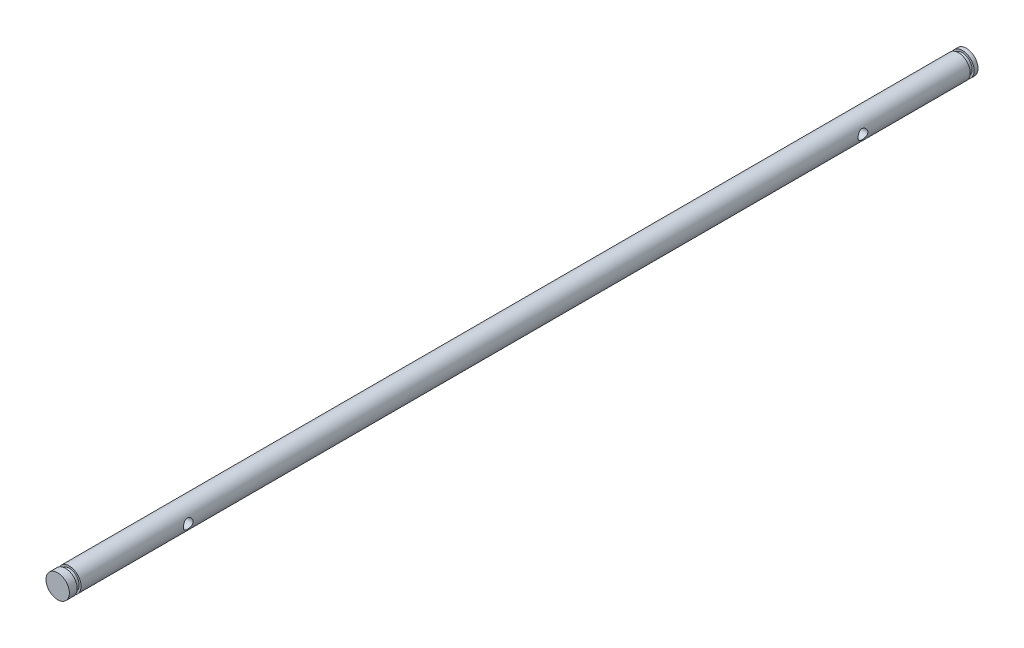
SolidWorks part; units mm, degrees
ref_plane "Front Plane" through (0, 0, 0) normal (0, 0, 1) x (1, 0, 0)
ref_plane "Top Plane" through (0, 0, 0) normal (0, 1, 0) x (1, 0, 0)
ref_plane "Right Plane" through (0, 0, 0) normal (1, 0, 0) x (0, 0, -1)
sketch "Sketch1" plane through (0, 0, 0) normal (0, 0, 1) x (1, 0, 0)
  circle A0 centre (0, 0) radius 3
  dimension "D1" = 6
extrude "Boss-Extrude1" add sketch "Sketch1" along normal blind 233
ref_axis "Axis1" through (0, 0, 233) along (0, 0, -1)
sketch "Sketch2" plane through (0, 0, 0) normal (0, 1, 0) x (1, 0, 0)
  line L0 (3, -233) -> (3, 0) construction
  line L1 (3, -1) -> (2.5, -1)
  line L2 (3, -1) -> (3, -2)
  line L3 (3, -2) -> (2.5, -2)
  line L4 (2.5, -1) -> (2.5, -2)
  line L5 (3, 0) -> (-3, 0) construction
  dimension "D1" = 1
  dimension "D2" = 0.5
  dimension "D3" = 1
revolve "Cut-Revolve1" cut sketch "Sketch2" angle 360 about axis through (0, 0, 233) along (0, 0, -1)
sketch "Sketch3" plane through (0, 0, 233) normal (0, 0, 1) x (1, 0, 0)
  line L0 (2.7, 1.3077) -> (2.7, -1.3077)
  circle A0 centre (0, 0) radius 3 construction
  circle A1 centre (0, 0) radius 3
  arc A2 (2.7, -1.3077) -> (2.7, 1.3077) centre (0, 0) ccw
  dimension "D2" = 2.7
  dimension "D1" = 0
extrude "Cut-Extrude1" cut sketch "Sketch3" against normal blind 0.5
ref_plane "Plane1" through (3.7, 0, 0) normal (1, 0, 0) x (0, 0, -1)
sketch "Sketch4" plane through (3.7, 0, 0) normal (1, 0, 0) x (0, 0, -1)
  line L0 (0, 0) -> (-29.5, 0) construction
  line L1 (-29.5, 0) -> (-202.5, 0) construction
  line L2 (0, -3) -> (0, 3) construction
  circle A0 centre (-202.5, 0) radius 1.5
  circle A1 centre (-29.5, 0) radius 1.5
  dimension "D1" = 3
  dimension "D2" = 173
  dimension "D3" = 29.5
hole_wizard "M3 Tapped Hole1" positions "3DSketch1" profile "Sketch5" tap size "M3" standard "ISO" end condition through all
sketch3d "3DSketch1"
  point P0 (3.7, 0, 29.5)
  point P3 (3.7, 0, 202.5)
sketch "Sketch5" plane through (3.7, 0, 29.5) normal (0, 1, 0) x (0, 0, -1)
  line L0 (0, 0) -> (0, 6.7)
  line L1 (0, 6.7) -> (1.25, 6.7)
  line L2 (1.25, 6.7) -> (1.25, 0)
  line L5 (1.25, 0) -> (0, 0)
  line L11 (0, -6.35) -> (0, 107.95) construction
  dimension "Thru Tap Drill Dia." = 2.5
  dimension "Thru Tap Drill Depth" = 6.7
sketch "Sketch6" plane through (0, 0, 0) normal (0, 1, 0) x (1, 0, 0)
  line L0 (3, -232.5) -> (3, -203.75) construction
  line L1 (3, -231) -> (2.5, -231)
  line L2 (3, -231) -> (3, -230)
  line L3 (3, -230) -> (2.5, -230)
  line L4 (2.5, -231) -> (2.5, -230)
  line L5 (-3, -233) -> (2.7, -233) construction
  dimension "D1" = 1
  dimension "D2" = 0.5
  dimension "D3" = 3
revolve "Cut-Revolve2" cut sketch "Sketch6" angle 360 about axis through (0, 0, 233) along (0, 0, -1)
sketch "Sketch7" plane through (0, 0, 232.5) normal (0, 0, 1) x (1, 0, 0)
  line L1 (2.7, 1.3077) -> (2.7, -1.3077)
  line L2 (2.7, 1.3077) -> (2.7, -1.3077)
  arc A1 (2.7, -1.3077) -> (2.7, 1.3077) centre (0, 0) ccw
  arc A2 (2.7, -1.3077) -> (2.7, 1.3077) centre (0, 0) ccw
  dimension "D1" = 0
extrude "Boss-Extrude2" add sketch "Sketch7" along normal up to surface (0.5 mm away) up to face at (-0.15, 0, 233)
